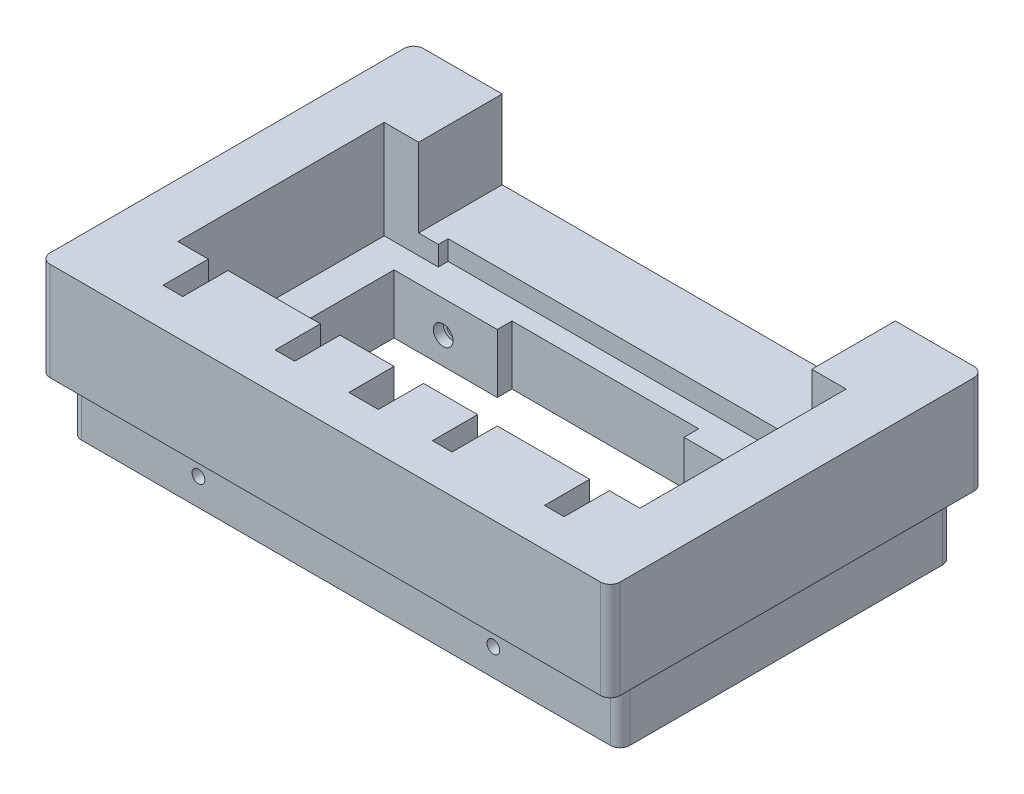
SolidWorks part; units mm, degrees
ref_plane "Front Plane" through (0, 0, 0) normal (0, 0, 1) x (1, 0, 0)
ref_plane "Top Plane" through (0, 0, 0) normal (0, 1, 0) x (1, 0, 0)
ref_plane "Right Plane" through (0, 0, 0) normal (1, 0, 0) x (0, 0, -1)
sketch "Sketch1" plane through (0, 0, 0) normal (0, 1, 0) x (1, 0, 0)
  line L1 (-139.5, 84.5) -> (139.5, 84.5)
  line L2 (-139.5, 84.5) -> (-139.5, -84.5)
  line L3 (-139.5, -84.5) -> (139.5, -84.5)
  line L4 (139.5, 84.5) -> (139.5, -84.5)
  line L5 (-139.5, 84.5) -> (139.5, -84.5) construction
  line L6 (-139.5, -84.5) -> (139.5, 84.5) construction
  point P0 (0, 0)
  dimension "D1" = 169
  dimension "D2" = 279
extrude "Boss-Extrude1" add sketch "Sketch1" against normal blind 30
sketch "Sketch2" plane through (0, 0, 0) normal (0, 1, 0) x (1, 0, 0)
  line L1 (-145, 95) -> (145, 95)
  line L2 (-145, 95) -> (-145, -95)
  line L3 (-145, -95) -> (145, -95)
  line L4 (145, 95) -> (145, -95)
  line L5 (-145, 95) -> (145, -95) construction
  line L6 (-145, -95) -> (145, 95) construction
  point P0 (0, 0)
  dimension "D1" = 190
  dimension "D2" = 290
extrude "Boss-Extrude2" add sketch "Sketch2" along normal blind 50
fillet "Fillet1" radius 5 4 edges at (-139.5, -15, -84.5) (139.5, -15, -84.5) (139.5, -15, 84.5) (-139.5, -15, 84.5)
fillet "Fillet2" radius 5 4 edges at (145, 25, -95) (145, 25, 95) (-145, 25, -95) (-145, 25, 95)
sketch "Sketch3" plane through (0, 50, 0) normal (0, 1, 0) x (1, 0, 0)
  line L1 (-117.5, 52.5) -> (117.5, 52.5)
  line L2 (-117.5, 52.5) -> (-117.5, -52.5)
  line L3 (-117.5, -52.5) -> (117.5, -52.5)
  line L4 (117.5, 52.5) -> (117.5, -52.5)
  line L5 (-117.5, 52.5) -> (117.5, -52.5) construction
  line L6 (-117.5, -52.5) -> (117.5, 52.5) construction
  point P0 (0, 0)
  dimension "D1" = 235
  dimension "D2" = 105
extrude "Cut-Extrude1" cut sketch "Sketch3" against normal blind 50
sketch "Sketch4" plane through (0, 0, 0) normal (0, 1, 0) x (1, 0, 0)
  line L1 (-100, 40) -> (100, 40)
  line L2 (-100, 40) -> (-100, -40)
  line L3 (-100, -40) -> (100, -40)
  line L4 (100, 40) -> (100, -40)
  line L5 (-100, 40) -> (100, -40) construction
  line L6 (-100, -40) -> (100, 40) construction
  point P0 (0, 0)
  dimension "D1" = 200
  dimension "D2" = 80
extrude "Cut-Extrude2" cut sketch "Sketch4" against normal blind 50
sketch "Sketch5" plane through (0, 50, 0) normal (0, 1, 0) x (1, 0, 0)
  line L0 (117.5, 52.5) -> (-117.5, 52.5) construction
  line L1 (-90, 52.5) -> (90, 52.5)
  line L2 (-90, 52.5) -> (-90, 57.5)
  line L3 (-90, 57.5) -> (90, 57.5)
  line L4 (90, 52.5) -> (90, 57.5)
  line L5 (0, 0) -> (0, 57.5) construction
  dimension "D1" = 5
  dimension "D2" = 180
extrude "Cut-Extrude3" cut sketch "Sketch5" against normal blind 50
sketch "Sketch6" plane through (0, 0, 0) normal (0, 1, 0) x (1, 0, 0)
  line L1 (-47.5, -47.5) -> (47.5, -47.5)
  line L2 (-47.5, -47.5) -> (-47.5, 47.5)
  line L3 (-47.5, 47.5) -> (47.5, 47.5)
  line L4 (47.5, -47.5) -> (47.5, 47.5)
  line L5 (-47.5, -47.5) -> (47.5, 47.5) construction
  line L6 (-47.5, 47.5) -> (47.5, -47.5) construction
  point P0 (0, 0)
  dimension "D1" = 95
extrude "Cut-Extrude4" cut sketch "Sketch6" against normal blind 50
sketch "Sketch7" plane through (0, 50, 0) normal (0, 1, 0) x (1, 0, 0)
  line L0 (-117.5, -52.5) -> (117.5, -52.5) construction
  line L1 (-7.5, -52.5) -> (7.5, -52.5)
  line L2 (-7.5, -52.5) -> (-7.5, -75.5)
  line L3 (-7.5, -75.5) -> (7.5, -75.5)
  line L4 (7.5, -52.5) -> (7.5, -75.5)
  line L5 (-117.5, -52.5) -> (117.5, -52.5) construction
  line L6 (45, -52.5) -> (35, -52.5)
  line L7 (45, -52.5) -> (45, -75.5)
  line L8 (45, -75.5) -> (35, -75.5)
  line L9 (35, -52.5) -> (35, -75.5)
  line L10 (0, 0) -> (0, -52.5) construction
  line L11 (-45, -52.5) -> (-35, -52.5)
  line L12 (-45, -52.5) -> (-45, -75.5)
  line L13 (-45, -75.5) -> (-35, -75.5)
  line L14 (-35, -52.5) -> (-35, -75.5)
  line L15 (92, -52.5) -> (102, -52.5)
  line L16 (92, -52.5) -> (92, -75.5)
  line L17 (92, -75.5) -> (102, -75.5)
  line L18 (102, -52.5) -> (102, -75.5)
  line L19 (-102, -52.5) -> (-92, -52.5)
  line L20 (-102, -52.5) -> (-102, -75.5)
  line L21 (-102, -75.5) -> (-92, -75.5)
  line L22 (-92, -52.5) -> (-92, -75.5)
  line L23 (-97, -52.5) -> (-97, -75.5) construction
  line L24 (-40, -52.5) -> (-40, -75.5) construction
  line L25 (40, -52.5) -> (40, -75.5) construction
  line L26 (97, -52.5) -> (97, -75.5) construction
  dimension "D1" = 15
  dimension "D2" = 23
  dimension "D3" = 10
  dimension "D4" = 194
  dimension "D5" = 80
extrude "Cut-Extrude5" cut sketch "Sketch7" against normal blind 50
sketch "Sketch8" plane through (0, 0, -84.5) normal (0, 0, -1) x (-1, 0, 0)
  line L0 (0, 0) -> (0, -30) construction
  line L1 (-134.5, 0) -> (134.5, 0) construction
  line L2 (-134.5, -30) -> (134.5, -30) construction
  line L3 (0, -16.25) -> (75, -16.25) construction
  line L4 (0, -16.25) -> (-75, -16.25) construction
  line L6 (-75, -13) -> (75, -13) construction
  line L7 (-140, 0) -> (140, 0) construction
  circle A0 centre (75, -16.25) radius 3.25
  circle A1 centre (-75, -16.25) radius 3.25
  dimension "D3" = 6.5
  dimension "D1" = 150
  dimension "D2" = 13
extrude "Cut-Extrude6" cut sketch "Sketch8" against normal through all
sketch "Sketch9" plane through (0, 0, 0) normal (0, 0, 1) x (1, 0, 0)
  circle A0 centre (-75, -16.25) radius 5
  circle A1 centre (75, -16.25) radius 5
  dimension "D1" = 10
  dimension "D2" = 10
extrude "Cut-Extrude7" cut sketch "Sketch9" against normal blind 45 and the other way blind 45
sketch "Sketch10" plane through (0, 50, 0) normal (0, 1, 0) x (1, 0, 0)
  line L1 (-0.5, -100) -> (0.5, -100)
  line L2 (-0.5, -100) -> (-0.5, 100)
  line L3 (-0.5, 100) -> (0.5, 100)
  line L4 (0.5, -100) -> (0.5, 100)
  line L5 (-0.5, -100) -> (0.5, 100) construction
  line L6 (-0.5, 100) -> (0.5, -100) construction
  point P0 (0, 0)
  dimension "D1" = 200
  dimension "D2" = 1
extrude "Cut-Extrude8" [suppressed] cut sketch "Sketch10" against normal blind 106.3
sketch "Sketch11" plane through (0, 0, -95) normal (0, 0, -1) x (-1, 0, 0)
  line L0 (-140, 50) -> (140, 50) construction
  line L1 (-100, 50) -> (100, 50)
  line L2 (-100, 50) -> (-100, 10)
  line L3 (-100, 10) -> (100, 10)
  line L4 (100, 50) -> (100, 10)
  line L5 (0, 0) -> (0, 71.4161) construction
  line L6 (-134.5, 0) -> (134.5, 0) construction
  dimension "D1" = 200
  dimension "D2" = 10
extrude "Cut-Extrude9" cut sketch "Sketch11" against normal blind 50
